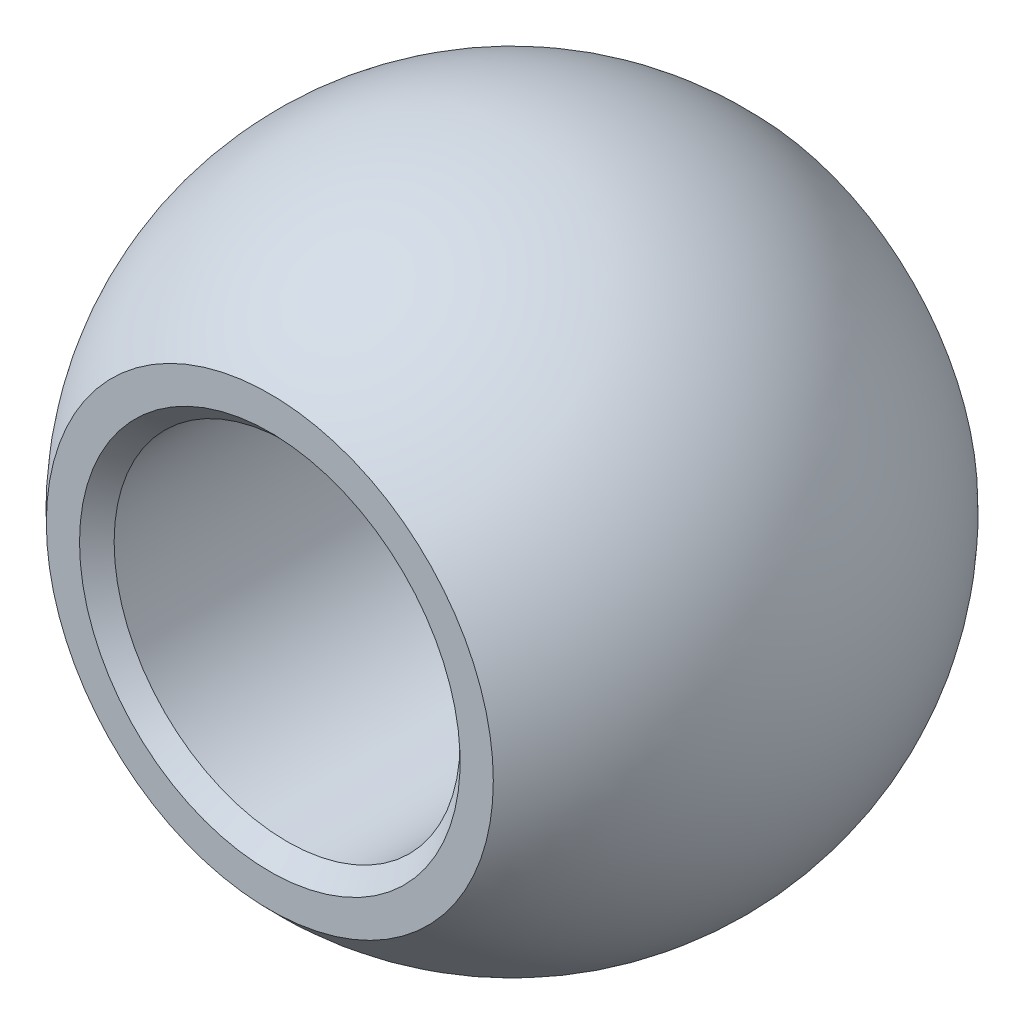
SolidWorks part; units mm, degrees
material "1060 Alloy"
ref_plane "Front Plane" through (0, 0, 0) normal (0, 0, 1) x (1, 0, 0)
ref_plane "Top Plane" through (0, 0, 0) normal (0, 1, 0) x (1, 0, 0)
ref_plane "Right Plane" through (0, 0, 0) normal (1, 0, 0) x (0, 0, -1)
sketch "Sketch1" plane through (0, 0, 0) normal (0, 0, 1) x (1, 0, 0)
  line L0 (0, 9.525) -> (0, -9.525)
  arc A0 (0, 9.525) -> (0, -9.525) centre (0, 0) cw
  dimension "D1" = 9.525
revolve "Revolve1" add sketch "Sketch1" angle 360 about L0
sketch "Sketch2" plane through (0, 0, 0) normal (1, 0, 0) x (0, 0, -1)
  line L3 (7, -9.525) -> (9.525, -9.525)
  line L4 (9.525, -9.525) -> (9.525, 9.525)
  line L5 (7, -9.525) -> (7, 9.525)
  line L6 (0, 0) -> (9.525, 0) construction
  line L7 (0, 0) -> (0, -9.525) construction
  line L8 (7, 9.525) -> (9.525, 9.525)
  line L9 (-7, -9.525) -> (-9.525, -9.525)
  line L10 (-9.525, -9.525) -> (-9.525, 9.525)
  line L11 (-7, 9.525) -> (-9.525, 9.525)
  line L12 (-7, -9.525) -> (-7, 9.525)
  circle A0 centre (0, 0) radius 9.525 construction
  point P12 (7, 0)
  dimension "D1" = 14
extrude "Cut-Extrude1" cut sketch "Sketch2" against normal through all both and the other way through all
sketch "Sketch3" plane through (0, 0, 0) normal (0, 0, 1) x (1, 0, 0)
  circle A0 centre (0, 0) radius 5
  dimension "D1" = 10
extrude "Cut-Extrude2" cut sketch "Sketch3" against normal through all both and the other way through all
chamfer "Chamfer1" distance 0.5 angle 45 2 edges at (5, 0, -7) (5, 0, 7)
